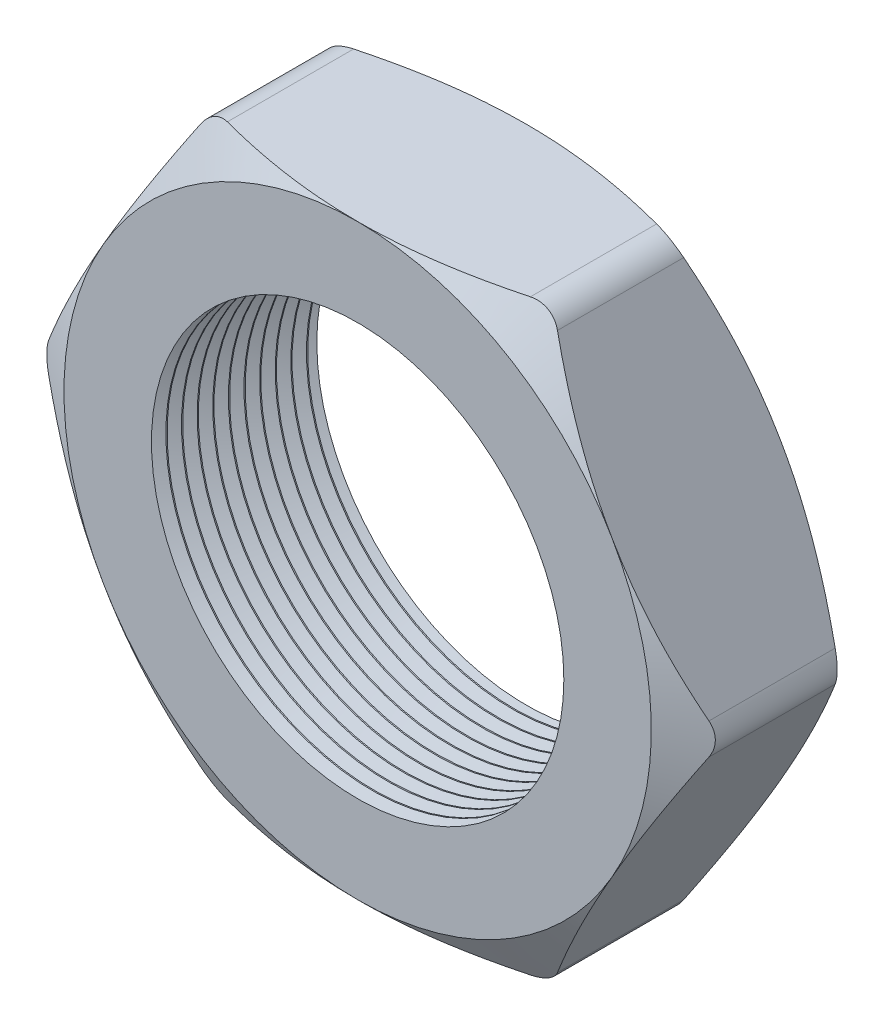
SolidWorks part; units mm, degrees
ref_plane "Front Plane" through (0, 0, 0) normal (0, 0, 1) x (1, 0, 0)
ref_plane "Top Plane" through (0, 0, 0) normal (0, 1, 0) x (1, 0, 0)
ref_plane "Right Plane" through (0, 0, 0) normal (1, 0, 0) x (0, 0, -1)
sketch "Sketch1" plane through (0, 0, 0) normal (0, 0, 1) x (1, 0, 0)
  line L1 (-13.7848, 0) -> (-6.8924, -11.938)
  line L2 (-6.8924, -11.938) -> (6.8924, -11.938)
  line L3 (6.8924, -11.938) -> (13.7848, 0)
  line L4 (13.7848, 0) -> (6.8924, 11.938)
  line L5 (6.8924, 11.938) -> (-6.8924, 11.938)
  line L6 (-6.8924, 11.938) -> (-13.7848, 0)
  circle A0 centre (0, 0) radius 11.938 construction
  circle A1 centre (0, 0) radius 8.382
  dimension "TS" = 16.764
  dimension "H" = 23.876
extrude "Extrude1" add sketch "Sketch1" along normal blind 6.858
sketch "Sketch2" plane through (0, 0, 6.858) normal (0, 0, 1) x (1, 0, 0)
  line L0 (6.8924, 11.938) -> (-6.8924, 11.938) construction
  circle A0 centre (0, 0) radius 11.938
extrude "Cut-Extrude1" cut sketch "Sketch2" against normal through all draft 60 flip side to cut
sketch "Sketch3" plane through (0, 0, 0) normal (0, 0, -1) x (-1, 0, 0)
  line L0 (-6.8924, 11.938) -> (6.8924, 11.938) construction
  circle A0 centre (0, 0) radius 11.938
extrude "Cut-Extrude2" cut sketch "Sketch3" against normal through all draft 60 flip side to cut
fillet "Fillet1" radius 1.27 6 edges at (13.7848, 0, 3.429) (6.8924, -11.938, 3.429) (-6.8924, -11.938, 3.429) (-13.7848, 0, 3.429) (-6.8924, 11.938, 3.429) (6.8924, 11.938, 3.429)
sketch "Sketch4" plane through (0, 0, 0) normal (0, 1, 0) x (1, 0, 0)
  line L0 (-8.382, -6.858) -> (-8.382, -6.2714)
  line L1 (-8.382, 0) -> (-8.382, -6.858) construction
  line L2 (-8.382, -6.2714) -> (-8.89, -6.5647)
  line L3 (-8.89, -6.5647) -> (-8.382, -6.858)
  dimension "D1" = 60
  dimension "D2" = 60
  dimension "D3" = 0.508
revolve "Cut-Revolve1" cut sketch "Sketch4" angle 360 about axis through (0, 0, 0) along (0, 0, 1)
pattern_linear "LPattern1" count 11 spacing 0.635 along (0, 0, -1) of "Cut-Revolve1"
